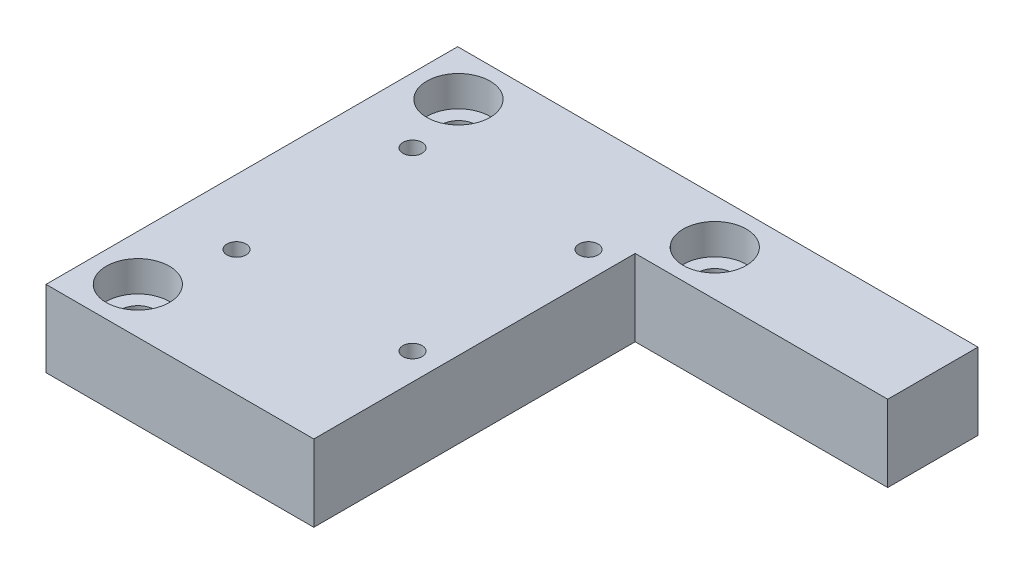
SolidWorks part; units mm, degrees
ref_plane "Front Plane" through (0, 0, 0) normal (0, 0, 1) x (1, 0, 0)
ref_plane "Top Plane" through (0, 0, 0) normal (0, 1, 0) x (1, 0, 0)
ref_plane "Right Plane" through (0, 0, 0) normal (1, 0, 0) x (0, 0, -1)
sketch "Sketch1" plane through (0, 0, 0) normal (0, 1, 0) x (1, 0, 0)
  line L0 (0, 0) -> (0, -53.8)
  line L1 (0, -53.8) -> (68, -53.8)
  line L2 (68, -53.8) -> (68, 0)
  line L3 (68, 0) -> (0, 0)
extrude "Boss-Extrude1" add sketch "Sketch1" against normal blind 10
sketch "Sketch2" plane through (0, -10, 0) normal (0, -1, 0) x (1, 0, 0)
  line L0 (35, 53.8) -> (35, 11.8)
  line L1 (35, 11.8) -> (68, 11.8)
  line L2 (68, 11.8) -> (68, 53.8)
  line L3 (68, 53.8) -> (35, 53.8)
extrude "Cut-Extrude1" cut sketch "Sketch2" against normal through all
hole_wizard "#2 Clearance Hole1" positions "Sketch4" profile "Sketch3" hole size "#2" standard "ANSI Inch"
sketch "Sketch4" plane through (0, -10, 0) normal (0, -1, 0) x (-1, 0, 0)
  point P0 (-31.5022, -14.4024)
  point P1 (-31.5, -37.4046)
  point P2 (-8.4978, -37.4024)
  point P3 (-8.5, -14.4002)
sketch "Sketch3" plane through (31.5022, -10, 14.4024) normal (1, 0, 0) x (0, 0, -1)
  line L0 (0, 0) -> (0, 10)
  line L1 (0, 10) -> (1.25, 10)
  line L2 (1.25, 10) -> (1.25, 0)
  line L5 (1.25, 0) -> (0, 0)
  line L11 (0, -6.35) -> (0, 107.95) construction
  dimension "Thru Hole Dia." = 2.5
  dimension "Thru Hole Depth" = 10
hole_wizard "CBORE for #8 Binding Head Machine Screw1" positions "Sketch6" profile "Sketch5" counterbore size "#8" standard "ANSI Inch"
sketch "Sketch6" plane through (0, 0, 0) normal (0, 1, 0) x (1, 0, 0)
  point P0 (6, -47.8)
  point P1 (6, -5.9)
  point P2 (39.5, -5.9)
sketch "Sketch5" plane through (6, 0, 47.8) normal (1, 0, 0) x (0, 0, 1)
  line L0 (0, 0) -> (0, 10)
  line L1 (0, 10) -> (2.25, 10)
  line L3 (2.25, 10) -> (2.25, 4)
  line L4 (2.25, 4) -> (4.125, 4)
  line L5 (4.125, 4) -> (4.125, 0)
  line L7 (4.125, 0) -> (0, 0)
  line L11 (0, -6.35) -> (0, 107.95) construction
  dimension "Thru Hole Dia." = 4.5
  dimension "Thru Hole Depth" = 10
  dimension "C'Bore Dia." = 8.25
  dimension "C'Bore Depth" = 4
